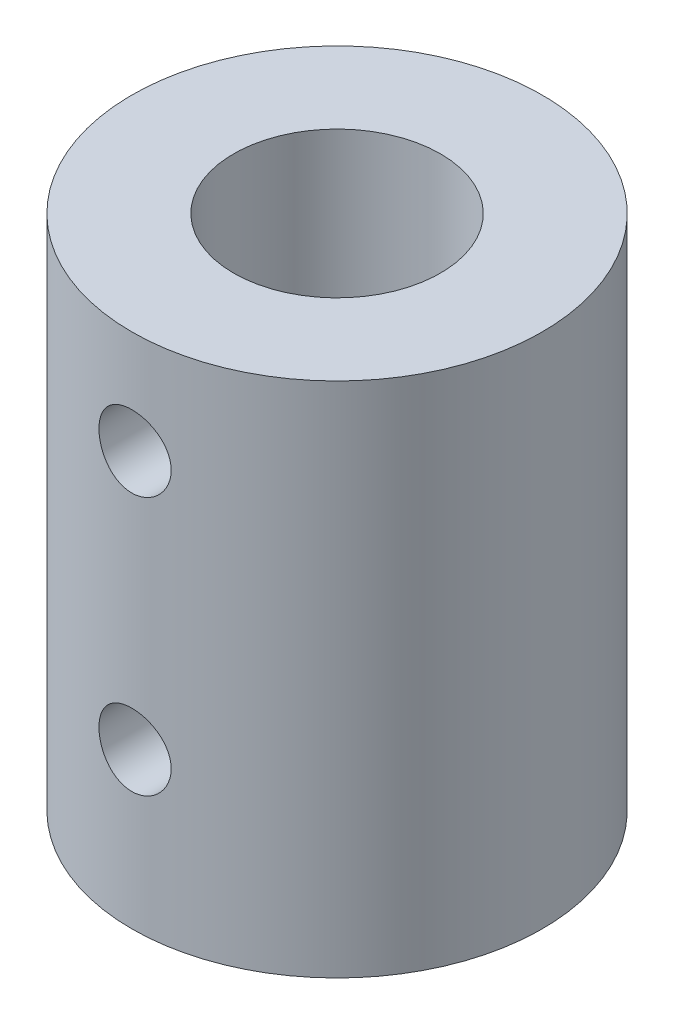
SolidWorks part; units mm, degrees
ref_plane "Front Plane" through (0, 0, 0) normal (0, 0, 1) x (1, 0, 0)
ref_plane "Top Plane" through (0, 0, 0) normal (0, 1, 0) x (1, 0, 0)
ref_plane "Right Plane" through (0, 0, 0) normal (1, 0, 0) x (0, 0, -1)
sketch "Sketch2" plane through (0, 0, 0) normal (0, 1, 0) x (1, 0, 0)
  circle A0 centre (0, 0) radius 7.9375
  dimension "D1" = 15.875
extrude "Boss-Extrude1" add sketch "Sketch2" along normal blind 20
sketch "Sketch3" plane through (0, 20, 0) normal (0, 1, 0) x (1, 0, 0)
  circle A0 centre (0, 0) radius 4
  dimension "D1" = 8
extrude "Cut-Extrude1" cut sketch "Sketch3" against normal blind 8
sketch "Sketch4" plane through (0, 0, 0) normal (0, -1, 0) x (1, 0, 0)
  line L0 (0, 0) -> (0, -9.3161) construction
  circle A0 centre (0, 0) radius 3
  dimension "D1" = 6
extrude "Cut-Extrude2" cut sketch "Sketch4" against normal blind 12
sketch "Sketch5" plane through (0, 20, 0) normal (0, 1, 0) x (1, 0, 0)
  line L0 (0, 0) -> (0, -7.9375) construction
  circle A0 centre (0, 0) radius 7.9375 construction
ref_plane "Plane1" through (0, 0, 7.9375) normal (0, 0, 1) x (1, 0, 0)
sketch "Sketch6" plane through (0, 0, 7.9375) normal (0, 0, 1) x (1, 0, 0)
  line L0 (0, 0) -> (0, 20) construction
  circle A0 centre (0, 6) radius 1.397
  circle A2 centre (0, 16) radius 1.397
  point P5 (0, 6)
  dimension "D3" = 2.794
  dimension "D4" = 2.794
  dimension "D1" = 20
  dimension "D2" = 6
  dimension "D5" = 16
extrude "Cut-Extrude3" cut sketch "Sketch6" against normal blind 6
